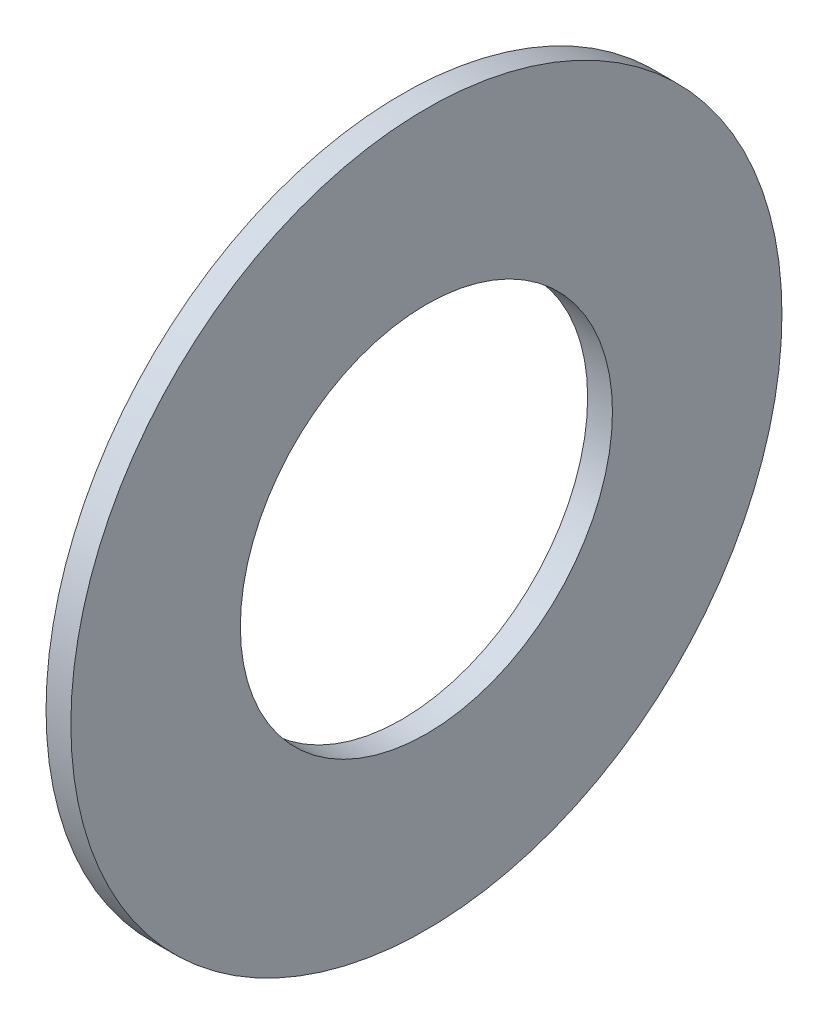
SolidWorks part; units mm, degrees
ref_plane "Front Plane" through (0, 0, 0) normal (0, 0, 1) x (1, 0, 0)
ref_plane "Top Plane" through (0, 0, 0) normal (0, 1, 0) x (1, 0, 0)
ref_plane "Right Plane" through (0, 0, 0) normal (1, 0, 0) x (0, 0, -1)
sketch "Sketch1" plane through (0, 0, 0) normal (0, 0, 1) x (1, 0, 0)
  line L0 (-20.2627, -2.0938) -> (34.2373, -2.0938) construction
  line L1 (-34.5911, 40.9062) -> (-31.5911, 40.9062)
  line L2 (-34.5911, 40.9062) -> (-34.5911, 20.4062)
  line L3 (-34.5911, 20.4062) -> (-31.5911, 20.4062)
  line L4 (-31.5911, 40.9062) -> (-31.5911, 20.4062)
  line L5 (-20.2627, -1.5938) -> (-20.2627, -2.5938) construction
  line L6 (34.2373, -4.3438) -> (34.2373, 0.1562) construction
  line L7 (-31.5911, 22.414) -> (-31.5911, -26.6016) construction
  dimension "D1" = 3
  dimension "D2" = 0
  dimension "D3" = 43
  dimension "D4" = 22.5
revolve "Revolve1" add sketch "Sketch1" angle 360 about L0
